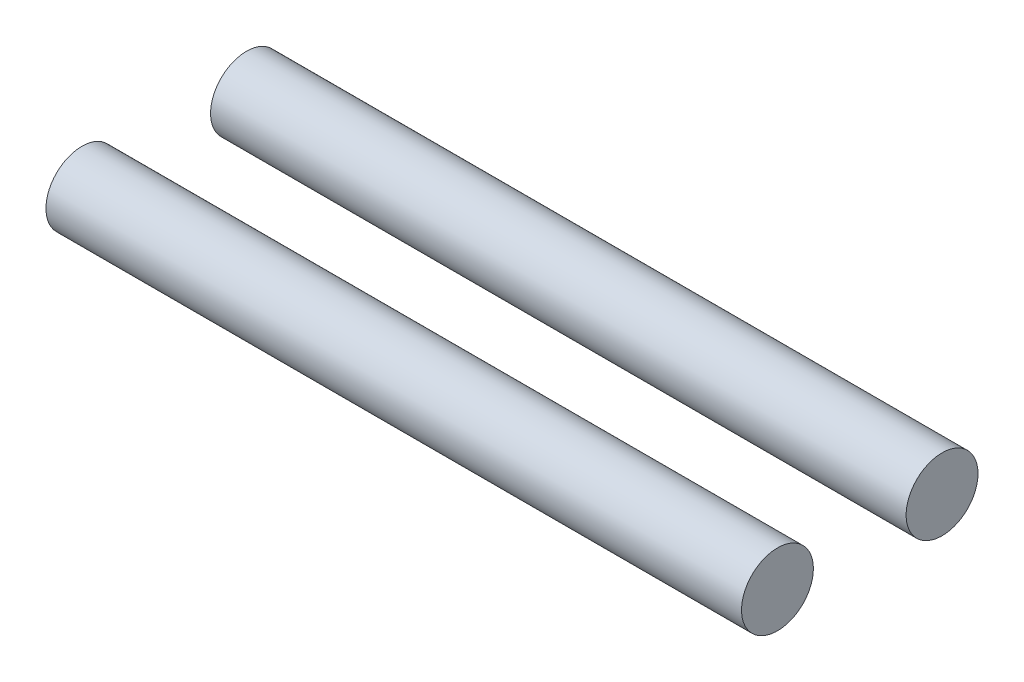
SolidWorks part; units mm, degrees
ref_plane "Спереди" through (0, 0, 0) normal (0, 0, 1) x (1, 0, 0)
ref_plane "Сверху" through (0, 0, 0) normal (0, 1, 0) x (1, 0, 0)
ref_plane "Справа" through (0, 0, 0) normal (1, 0, 0) x (0, 0, -1)
sketch "Эскиз1" plane through (0, 0, 0) normal (0, 0, 1) x (1, 0, 0)
  line L0 (0, 0) -> (-30, 0)
  dimension "D1" = 30
sketch "Эскиз2" plane through (0, 0, 0) normal (1, 0, 0) x (0, 0, -1)
  line L0 (0, 0) -> (7.1, 0) construction
  circle A0 centre (0, 0) radius 1.55
  circle A1 centre (7.1, 0) radius 1.55
  dimension "D1" = 3.1
  dimension "D3" = 3.1
  dimension "D2" = 7.1
sweep "По траектории1" add profiles "Эскиз2" path "Эскиз1"
